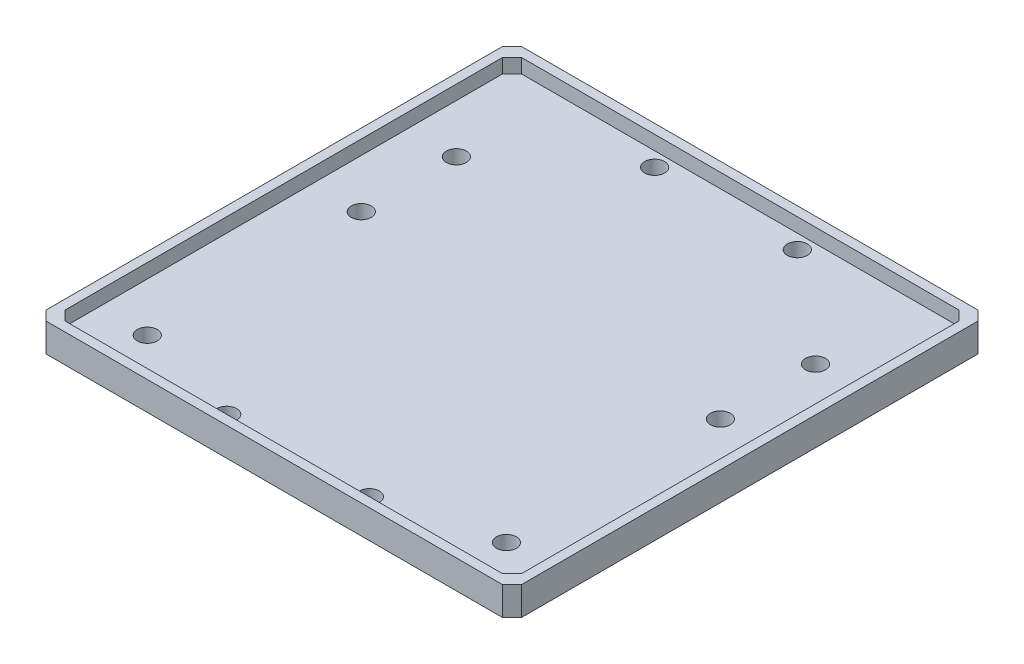
SolidWorks part; units mm, degrees
ref_plane "Front Plane" through (0, 0, 0) normal (0, 0, 1) x (1, 0, 0)
ref_plane "Top Plane" through (0, 0, 0) normal (0, 1, 0) x (1, 0, 0)
ref_plane "Right Plane" through (0, 0, 0) normal (1, 0, 0) x (0, 0, -1)
sketch "Sketch4" plane through (0, 0, 0) normal (0, 1, 0) x (1, 0, 0)
  line L3 (89.4442, -163.4248) -> (-10.5558, -163.4248)
  line L5 (89.4442, -63.4248) -> (-10.5558, -63.4248)
  line L6 (-10.5558, -163.4248) -> (-10.5558, -63.4248)
  line L7 (89.4442, -163.4248) -> (89.4442, -63.4248)
  circle A0 centre (1.6848, -87.3604) radius 2.1
  circle A1 centre (1.6848, -107.3604) radius 2.1
  circle A2 centre (1.6848, -152.3604) radius 2.1
  circle A3 centre (77.2035, -87.3604) radius 2.1
  circle A4 centre (77.2035, -107.3604) radius 2.1
  circle A5 centre (77.2035, -152.3604) radius 2.1
  circle A8 centre (54.4442, -158.4248) radius 2.1
  circle A9 centre (24.4442, -158.4248) radius 2.1
  circle A10 centre (54.4442, -68.4248) radius 2.1
  circle A11 centre (24.4442, -68.4248) radius 2.1
  point P0 (0, 0)
  dimension "D1" = 100
sketch "Sketch6" plane through (0, 0, 0) normal (0, 1, 0) x (1, 0, 0)
  line L0 (39.4442, -63.4248) -> (39.4442, -163.4248) construction
  line L1 (-10.5558, -63.4248) -> (89.4442, -63.4248)
  line L2 (-10.5558, -63.4248) -> (-10.5558, -163.4248)
  line L3 (-10.5558, -163.4248) -> (89.4442, -163.4248)
  line L4 (89.4442, -63.4248) -> (89.4442, -163.4248)
  circle A0 centre (1.6848, -87.3604) radius 2.1
  circle A1 centre (1.6848, -107.3604) radius 2.1
  circle A2 centre (1.6848, -152.3604) radius 2.1
  circle A3 centre (24.4442, -158.4248) radius 2.1
  circle A4 centre (24.4442, -68.4248) radius 2.1
  circle A5 centre (54.4442, -158.4248) radius 2.1
  circle A6 centre (77.2035, -152.3604) radius 2.1
  circle A7 centre (77.2035, -107.3604) radius 2.1
  circle A8 centre (77.2035, -87.3604) radius 2.1
  circle A9 centre (54.4442, -68.4248) radius 2.1
extrude "Boss-Extrude2" add sketch "Sketch6" along normal blind 3
sketch "Sketch7" plane through (0, 3, 0) normal (0, 1, 0) x (1, 0, 0)
  line L0 (89.4442, -63.4248) -> (-10.5558, -63.4248) construction
  line L1 (-10.5558, -163.4248) -> (-8.5558, -163.4248)
  line L2 (-10.5558, -163.4248) -> (-10.5558, -63.4248)
  line L3 (-10.5558, -63.4248) -> (-8.5558, -63.4248)
  line L4 (-8.5558, -163.4248) -> (-8.5558, -63.4248)
  line L5 (39.4442, -63.4248) -> (39.4442, -163.4248) construction
  line L6 (-10.5558, -163.4248) -> (89.4442, -163.4248) construction
  line L7 (89.4442, -63.4248) -> (87.4442, -63.4248)
  line L8 (87.4442, -163.4248) -> (87.4442, -63.4248)
  line L9 (89.4442, -163.4248) -> (87.4442, -163.4248)
  line L10 (89.4442, -163.4248) -> (89.4442, -63.4248)
  line L12 (-8.5558, -63.4248) -> (87.4442, -63.4248)
  line L13 (-8.5558, -63.4248) -> (-8.5558, -65.4248)
  line L14 (-8.5558, -65.4248) -> (87.4442, -65.4248)
  line L15 (87.4442, -63.4248) -> (87.4442, -65.4248)
  line M16 (-10.5558, -163.4248) -> (89.4442, -163.4248)
  line M17 (89.4442, -163.4248) -> (89.4442, -63.4248)
  line M18 (89.4442, -63.4248) -> (-10.5558, -63.4248)
  dimension "D1" = 2
  dimension "D2" = 0
  dimension "D3" = 2
extrude "Boss-Extrude3" add sketch "Sketch7" along normal blind 3 contours L5 L14 L8 M18 | L5 L12 L4 L14 | L8 M16 M17 M18
sketch "Sketch8" plane through (0, 3, 0) normal (0, 1, 0) x (1, 0, 0)
  line L0 (87.4442, -163.4248) -> (87.4442, -65.4248) construction
  line L1 (-8.5558, -163.4248) -> (87.4442, -163.4248)
  line L2 (-8.5558, -163.4248) -> (-8.5558, -161.4248)
  line L3 (-8.5558, -161.4248) -> (87.4442, -161.4248)
  line L4 (87.4442, -163.4248) -> (87.4442, -161.4248)
  dimension "D1" = 2
extrude "Boss-Extrude4" add sketch "Sketch8" along normal blind 3
chamfer "Chamfer1" distance 2 angle 45 4 edges at (-10.5558, 3, 63.4248) (-10.5558, 3, 163.4248) (89.4442, 3, 163.4248) (89.4442, 3, 63.4248)
sketch "Sketch9" plane through (0, 3, 0) normal (0, 1, 0) x (1, 0, 0)
  line L0 (-6.5558, -65.4248) -> (-8.5558, -67.4248)
  line L1 (-8.5558, -65.4248) -> (87.4442, -65.4248) construction
  line L2 (-8.5558, -161.4248) -> (-8.5558, -65.4248) construction
  line L3 (-8.5558, -67.4248) -> (-8.5558, -65.4248)
  line L4 (-8.5558, -65.4248) -> (-6.5558, -65.4248)
  line L5 (39.4442, -65.4248) -> (39.4442, -76.8168) construction
  line L6 (87.4442, -113.4248) -> (79.7492, -113.4248) construction
  line L7 (87.4442, -161.4248) -> (87.4442, -65.4248) construction
  line L8 (87.4442, -67.4248) -> (87.4442, -65.4248)
  line L9 (85.4442, -65.4248) -> (87.4442, -67.4248)
  line L10 (87.4442, -65.4248) -> (85.4442, -65.4248)
  line L11 (85.4442, -161.4248) -> (87.4442, -159.4248)
  line L12 (87.4442, -161.4248) -> (85.4442, -161.4248)
  line L13 (87.4442, -159.4248) -> (87.4442, -161.4248)
  line L14 (-8.5558, -159.4248) -> (-8.5558, -161.4248)
  line L15 (-6.5558, -161.4248) -> (-8.5558, -159.4248)
  line L16 (-8.5558, -161.4248) -> (-6.5558, -161.4248)
  dimension "D1" = 2
  dimension "D2" = 2
extrude "Boss-Extrude5" add sketch "Sketch9" along normal blind 3
